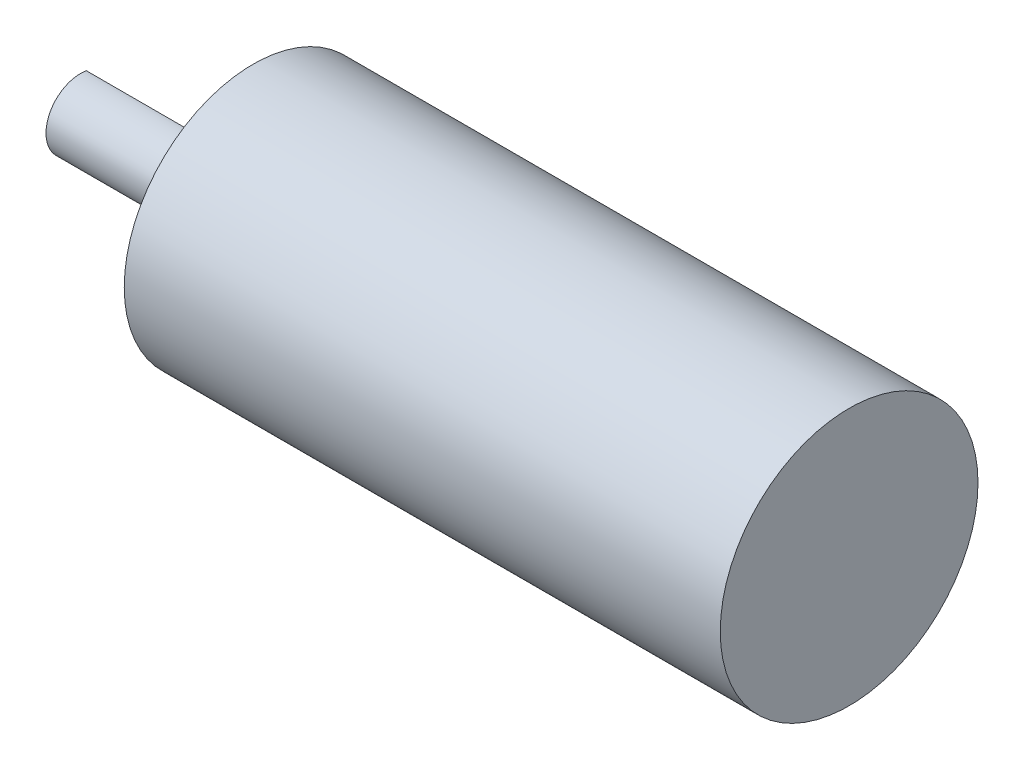
SolidWorks part; units mm, degrees
ref_plane "Front Plane" through (0, 0, 0) normal (0, 0, 1) x (1, 0, 0)
ref_plane "Top Plane" through (0, 0, 0) normal (0, 1, 0) x (1, 0, 0)
ref_plane "Right Plane" through (0, 0, 0) normal (1, 0, 0) x (0, 0, -1)
sketch "Sketch1" plane through (0, 0, 0) normal (1, 0, 0) x (0, 0, -1)
  circle A0 centre (0, 0) radius 11.2
  dimension "D1" = 22.4
extrude "Boss-Extrude1" add sketch "Sketch1" against normal blind 51.8
sketch "Sketch2" plane through (-51.8, 0, 0) normal (-1, 0, 0) x (0, 0, 1)
  line L0 (-0.5, 2.958) -> (-0.5, -2.958)
  arc A0 (-0.5, -2.958) -> (-0.5, 2.958) centre (0, 0) ccw
  dimension "D1" = 6
  dimension "D2" = 0.5
extrude "Boss-Extrude2" add sketch "Sketch2" along normal blind 15
